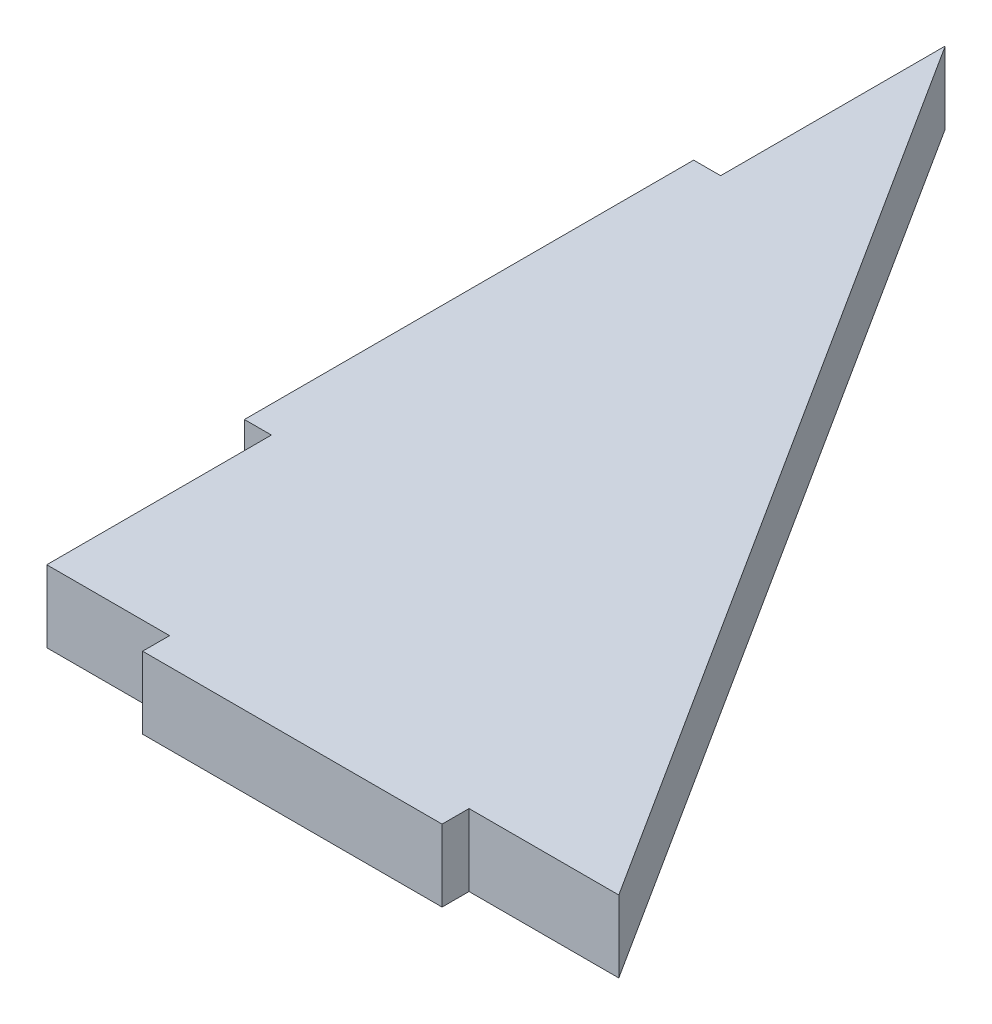
SolidWorks part; units mm, degrees
ref_plane "Front Plane" through (0, 0, 0) normal (0, 0, 1) x (1, 0, 0)
ref_plane "Top Plane" through (0, 0, 0) normal (0, 1, 0) x (1, 0, 0)
ref_plane "Right Plane" through (0, 0, 0) normal (1, 0, 0) x (0, 0, -1)
sketch "Sketch1" plane through (0, 0, 0) normal (0, 1, 0) x (1, 0, 0)
  line L0 (0, 0) -> (95.5, 0)
  line L1 (-55, 0) -> (55, 0) construction
  line L2 (0, 0) -> (0, 150)
  line L3 (0, -55) -> (0, 55) construction
  line L4 (0, 150) -> (95.5, 0)
  line L6 (20.5, 4.5) -> (70.5, 4.5)
  line L7 (20.5, 4.5) -> (20.5, -4.5)
  line L8 (20.5, -4.5) -> (70.5, -4.5)
  line L9 (70.5, 4.5) -> (70.5, -4.5)
  line L10 (20.5, 4.5) -> (70.5, -4.5) construction
  line L11 (20.5, -4.5) -> (70.5, 4.5) construction
  line L12 (-4.5, 112.5) -> (4.5, 112.5)
  line L13 (-4.5, 112.5) -> (-4.5, 37.5)
  line L14 (-4.5, 37.5) -> (4.5, 37.5)
  line L15 (4.5, 112.5) -> (4.5, 37.5)
  line L16 (-4.5, 112.5) -> (4.5, 37.5) construction
  line L17 (-4.5, 37.5) -> (4.5, 112.5) construction
  point P5 (45.5, 0)
  point P13 (0, 75)
  dimension "D1" = 150
  dimension "D2" = 95.5
  dimension "D3" = 9
  dimension "D4" = 50
  dimension "D5" = 20.5
  dimension "D6" = 9
  dimension "D7" = 75
  dimension "D8" = 37.5
extrude "Boss-Extrude1" add sketch "Sketch1" along normal blind 12 contours L13 L14 L2 L12 | L12 L15 L14 L2 L0 L7 L6 L9 L4 | L9 L0 L7 L8 | L9 L6 L7 L0 | L15 L12 L2 L14
